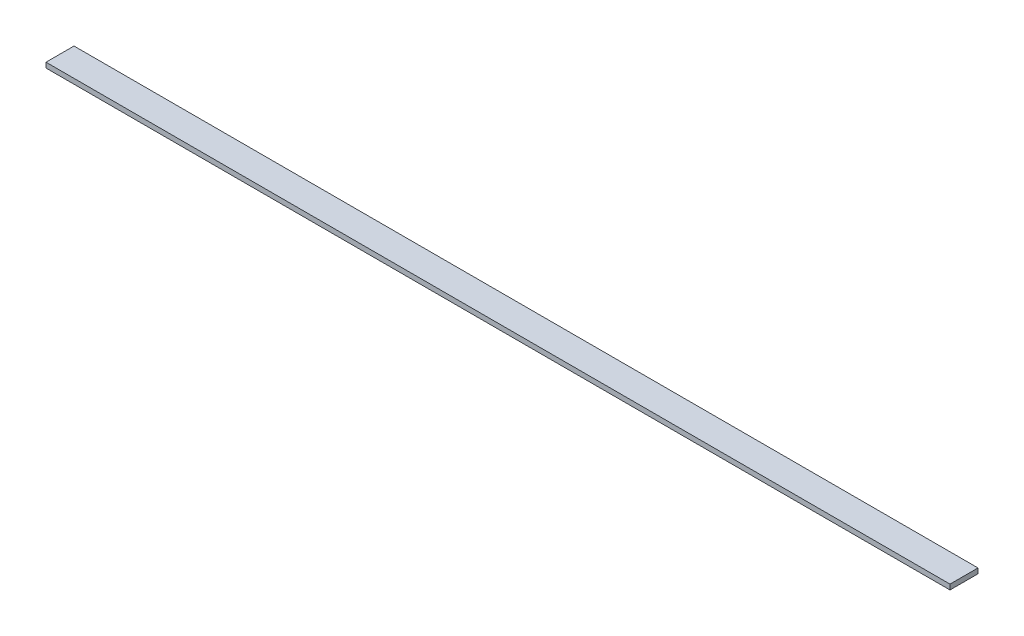
SolidWorks part; units mm, degrees
ref_plane "Front Plane" through (0, 0, 0) normal (0, 0, 1) x (1, 0, 0)
ref_plane "Top Plane" through (0, 0, 0) normal (0, 1, 0) x (1, 0, 0)
ref_plane "Right Plane" through (0, 0, 0) normal (1, 0, 0) x (0, 0, -1)
sketch "Sketch1" plane through (0, 0, 0) normal (0, 1, 0) x (1, 0, 0)
  line L0 (0, 0) -> (0, -139.7)
  line L1 (0, 0) -> (4508.5, 0)
  line L3 (0, -139.7) -> (4508.5, -139.7)
  line L5 (4508.5, 0) -> (4508.5, -139.7)
  dimension "D1" = 4508.5
  dimension "D2" = 139.7
extrude "Boss-Extrude1" add sketch "Sketch1" along normal blind 25.4
